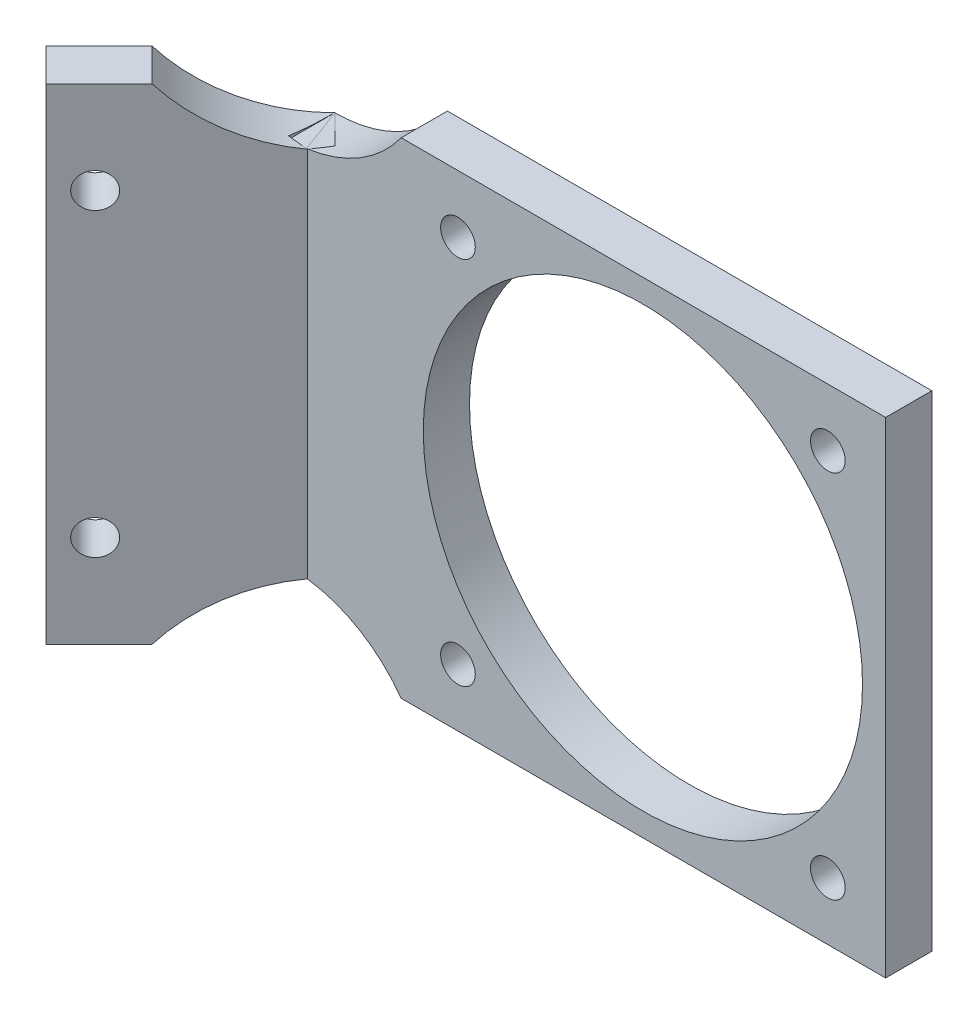
SolidWorks part; units mm, degrees
ref_plane "Front Plane" through (0, 0, 0) normal (0, 0, 1) x (1, 0, 0)
ref_plane "Top Plane" through (0, 0, 0) normal (0, 1, 0) x (1, 0, 0)
ref_plane "Right Plane" through (0, 0, 0) normal (1, 0, 0) x (0, 0, -1)
sketch "Sketch1" plane through (0, 0, 0) normal (0, 1, 0) x (1, 0, 0)
  line L0 (0, 0) -> (51.6569, 0)
  line L1 (51.6569, 0) -> (51.6569, -4)
  line L2 (51.6569, -4) -> (1.6569, -4)
  line L3 (1.6569, -4) -> (-9.6569, -15.3137)
  line L4 (-9.6569, -15.3137) -> (-12.4853, -12.4853)
  line L5 (-12.4853, -12.4853) -> (0, 0)
  line L6 (0, 0) -> (1.6569, -4) construction
  dimension "D1" = 135
  dimension "D2" = 67.5
  dimension "D3" = 4
  dimension "D4" = 50
  dimension "D5" = 16
extrude "Boss-Extrude1" add sketch "Sketch1" along normal blind 42
sketch "Sketch2" plane through (2.8284, 0, 2.8284) normal (0.7071, 0, 0.7071) x (0.7071, 0, -0.7071)
  line L0 (-14.6569, 8) -> (-14.6569, 0) construction
  line L1 (-17.6569, 0) -> (-1.6569, 0) construction
  line L2 (-14.6569, 34) -> (-14.6569, 42) construction
  line L3 (-17.6569, 42) -> (-1.6569, 42) construction
  line L4 (-17.6569, 42) -> (-17.6569, 0) construction
  circle A0 centre (-14.6569, 34) radius 1.5
  circle A1 centre (-14.6569, 8) radius 1.5
  dimension "D2" = 3
  dimension "D3" = 26
  dimension "D1" = 3
extrude "Cut-Extrude1" cut sketch "Sketch2" against normal up to next
sketch "Sketch3" plane through (0, 0, 4) normal (0, 0, 1) x (1, 0, 0)
  line L0 (14.6569, 37) -> (46.6569, 37) construction
  line L1 (46.6569, 37) -> (46.6569, 5) construction
  line L2 (46.6569, 5) -> (14.6569, 5) construction
  line L3 (14.6569, 5) -> (14.6569, 37) construction
  line L4 (46.6569, 37) -> (46.6569, 42) construction
  line L5 (1.6569, 42) -> (51.6569, 42) construction
  line L6 (46.6569, 37) -> (51.6569, 37) construction
  line L7 (51.6569, 42) -> (51.6569, 0) construction
  line L8 (46.6569, 5) -> (46.6569, 0) construction
  line L9 (1.6569, 0) -> (51.6569, 0) construction
  line L10 (30.6569, 21) -> (46.6569, 21) construction
  line L11 (30.6569, 21) -> (30.6569, 37) construction
  circle A0 centre (14.6569, 37) radius 1.5
  circle A1 centre (46.6569, 37) radius 1.5
  circle A2 centre (46.6569, 5) radius 1.5
  circle A3 centre (14.6569, 5) radius 1.5
  circle A4 centre (30.6569, 21) radius 19
  dimension "D1" = 3
  dimension "D3" = 38
  dimension "D2" = 32
extrude "Cut-Extrude2" cut sketch "Sketch3" against normal up to next
sketch "Sketch6" plane through (0, 0, 0) normal (-0.7071, 0, -0.7071) x (-0.7071, 0, 0.7071)
  line L1 (0, 42) -> (17.6569, 42) construction
  line L2 (0, 42) -> (0, 0) construction
  line L4 (0, 0) -> (17.6569, 0) construction
  line L5 (0, 5) -> (0, 0)
  line L6 (0, 0) -> (11.1803, 0)
  line L7 (0, 37) -> (0, 42)
  line L8 (0, 42) -> (11.1803, 42)
  arc A0 (0, 37) -> (11.1803, 42) centre (0, 52) ccw
  arc A1 (0, 5) -> (11.1803, 0) centre (0, -10) cw
  dimension "D1" = 15
  dimension "D2" = 10
  dimension "D3" = 10
extrude "Cut-Extrude3" cut sketch "Sketch6" against normal up to surface (4 mm away) up to face at (-6.4749, 8, 12.1317)
sketch "Sketch7" plane through (0, 0, 0) normal (0, 0, -1) x (-1, 0, 0)
  line L0 (-51.6569, 42) -> (0, 42) construction
  line L1 (-51.6569, 0) -> (0, 0) construction
  line L2 (-9.7468, 42) -> (0, 42)
  line L3 (0, 42) -> (0, 37)
  line L4 (-9.7468, 0) -> (0, 0)
  line L5 (0, 0) -> (0, 5)
  line L6 (0, 37) -> (0, 5) construction
  arc A0 (0, 37) -> (-9.7468, 42) centre (0, 49) cw
  arc A1 (0, 5) -> (-9.7468, 0) centre (0, -7) ccw
  ellipse E0 centre (0, 52) end of major axis (0, 37) minor radius 10.6066 (0, 37) -> (7.9057, 42) ccw construction
  dimension "D1" = 7
  dimension "D2" = 7
extrude "Cut-Extrude4" cut sketch "Sketch7" against normal up to surface (4 mm away) up to face at (49.6569, 21, 4)
equation "\"D2@Sketch1\"=\"D1@Sketch1\"/2"
equation "\"D3@Sketch6\"=\"D2@Sketch6\""
equation "\"D2@Sketch7\"=\"D1@Sketch7\""
